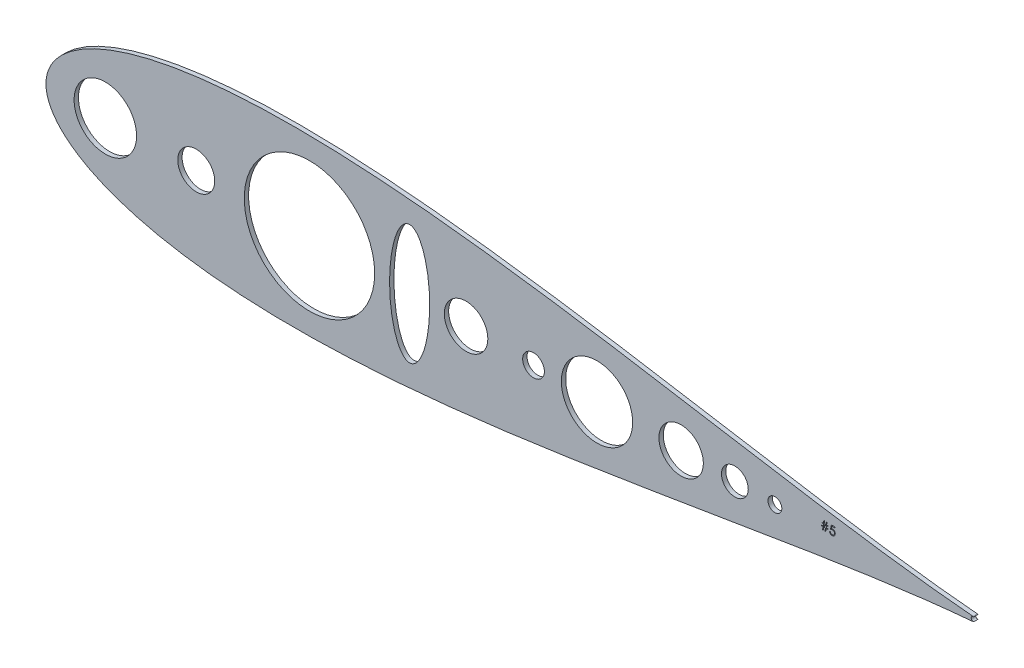
SolidWorks part; units mm, degrees
material "Balsa"
ref_plane "Front Plane" through (0, 0, 0) normal (0, 0, 1) x (1, 0, 0)
ref_plane "Top Plane" through (0, 0, 0) normal (0, 1, 0) x (1, 0, 0)
ref_plane "Right Plane" through (0, 0, 0) normal (1, 0, 0) x (0, 0, -1)
sketch "Sketch2" plane through (0, 0, 0) normal (0, 0, 1) x (1, 0, 0)
  line L0 (368.5896, 3.2313) -> (368.5896, 2.9057)
  line L1 (368.5896, 2.9057) -> (367.6188, 2.9057)
  line L2 (367.6188, 2.9057) -> (367.3552, 1.1472)
  line L3 (367.3552, 1.1472) -> (366.9614, 1.1472)
  line L4 (366.9614, 1.1472) -> (367.2249, 2.9057)
  line L5 (367.2249, 2.9057) -> (366.1859, 2.9057)
  line L6 (366.1859, 2.9057) -> (365.9224, 1.1472)
  line L7 (365.9224, 1.1472) -> (365.5285, 1.1472)
  line L8 (365.5285, 1.1472) -> (365.7921, 2.9057)
  line L9 (365.7921, 2.9057) -> (364.9424, 2.9057)
  line L10 (364.9424, 2.9057) -> (364.9424, 3.2313)
  line L11 (364.9424, 3.2313) -> (365.841, 3.2313)
  line L12 (365.841, 3.2313) -> (366.017, 4.4036)
  line L13 (366.017, 4.4036) -> (365.0727, 4.4036)
  line L14 (365.0727, 4.4036) -> (365.0727, 4.7293)
  line L15 (365.0727, 4.7293) -> (366.0659, 4.7293)
  line L16 (366.0659, 4.7293) -> (366.3101, 6.3575)
  line L17 (366.3101, 6.3575) -> (366.7029, 6.3575)
  line L18 (366.7029, 6.3575) -> (366.4587, 4.7293)
  line L19 (366.4587, 4.7293) -> (367.4987, 4.7293)
  line L20 (367.4987, 4.7293) -> (367.7429, 6.3575)
  line L21 (367.7429, 6.3575) -> (368.1357, 6.3575)
  line L22 (368.1357, 6.3575) -> (367.8915, 4.7293)
  line L23 (367.8915, 4.7293) -> (368.7198, 4.7293)
  line L24 (368.7198, 4.7293) -> (368.7198, 4.4036)
  line L25 (368.7198, 4.4036) -> (367.8426, 4.4036)
  line L26 (367.8426, 4.4036) -> (367.6676, 3.2313)
  line L27 (367.6676, 3.2313) -> (368.5896, 3.2313)
  line L28 (367.4498, 4.4036) -> (366.4098, 4.4036)
  line L29 (366.4098, 4.4036) -> (366.2348, 3.2313)
  line L30 (366.2348, 3.2313) -> (367.2738, 3.2313)
  line L31 (367.2738, 3.2313) -> (367.4498, 4.4036)
  line L32 (372.7578, 6.2272) -> (372.7578, 5.7062)
  line L33 (372.7578, 5.7062) -> (371.0298, 5.7062)
  line L34 (371.0298, 5.7062) -> (370.7561, 4.37)
  line L35 (370.7561, 4.37) -> (370.9179, 4.4128)
  line L36 (370.9179, 4.4128) -> (371.0716, 4.4443)
  line L37 (371.0716, 4.4443) -> (371.2171, 4.4627)
  line L38 (371.2171, 4.4627) -> (371.3545, 4.4688)
  line L39 (371.3545, 4.4688) -> (371.5244, 4.4616)
  line L40 (371.5244, 4.4616) -> (371.6872, 4.4392)
  line L41 (371.6872, 4.4392) -> (371.8419, 4.4026)
  line L42 (371.8419, 4.4026) -> (371.9895, 4.3517)
  line L43 (371.9895, 4.3517) -> (372.1289, 4.2866)
  line L44 (372.1289, 4.2866) -> (372.2602, 4.2062)
  line L45 (372.2602, 4.2062) -> (372.3843, 4.1116)
  line L46 (372.3843, 4.1116) -> (372.5013, 4.0017)
  line L47 (372.5013, 4.0017) -> (372.6072, 3.8806)
  line L48 (372.6072, 3.8806) -> (372.6988, 3.7523)
  line L49 (372.6988, 3.7523) -> (372.7771, 3.615)
  line L50 (372.7771, 3.615) -> (372.8402, 3.4705)
  line L51 (372.8402, 3.4705) -> (372.8901, 3.3168)
  line L52 (372.8901, 3.3168) -> (372.9247, 3.155)
  line L53 (372.9247, 3.155) -> (372.946, 2.9851)
  line L54 (372.946, 2.9851) -> (372.9532, 2.807)
  line L55 (372.9532, 2.807) -> (372.9491, 2.6828)
  line L56 (372.9491, 2.6828) -> (372.9389, 2.5607)
  line L57 (372.9389, 2.5607) -> (372.9206, 2.4416)
  line L58 (372.9206, 2.4416) -> (372.8952, 2.3246)
  line L59 (372.8952, 2.3246) -> (372.8626, 2.2106)
  line L60 (372.8626, 2.2106) -> (372.8229, 2.0997)
  line L61 (372.8229, 2.0997) -> (372.7751, 1.9908)
  line L62 (372.7751, 1.9908) -> (372.7211, 1.884)
  line L63 (372.7211, 1.884) -> (372.6611, 1.7822)
  line L64 (372.6611, 1.7822) -> (372.595, 1.6866)
  line L65 (372.595, 1.6866) -> (372.5247, 1.597)
  line L66 (372.5247, 1.597) -> (372.4494, 1.5136)
  line L67 (372.4494, 1.5136) -> (372.368, 1.4362)
  line L68 (372.368, 1.4362) -> (372.2815, 1.365)
  line L69 (372.2815, 1.365) -> (372.191, 1.2999)
  line L70 (372.191, 1.2999) -> (372.0943, 1.2408)
  line L71 (372.0943, 1.2408) -> (371.9935, 1.1879)
  line L72 (371.9935, 1.1879) -> (371.8887, 1.1432)
  line L73 (371.8887, 1.1432) -> (371.7809, 1.1045)
  line L74 (371.7809, 1.1045) -> (371.6689, 1.0729)
  line L75 (371.6689, 1.0729) -> (371.5529, 1.0485)
  line L76 (371.5529, 1.0485) -> (371.4328, 1.0312)
  line L77 (371.4328, 1.0312) -> (371.3087, 1.02)
  line L78 (371.3087, 1.02) -> (371.1815, 1.017)
  line L79 (371.1815, 1.017) -> (371.0298, 1.0231)
  line L80 (371.0298, 1.0231) -> (370.8843, 1.0424)
  line L81 (370.8843, 1.0424) -> (370.7449, 1.0729)
  line L82 (370.7449, 1.0729) -> (370.6116, 1.1167)
  line L83 (370.6116, 1.1167) -> (370.4844, 1.1727)
  line L84 (370.4844, 1.1727) -> (370.3633, 1.2419)
  line L85 (370.3633, 1.2419) -> (370.2473, 1.3223)
  line L86 (370.2473, 1.3223) -> (370.1384, 1.4159)
  line L87 (370.1384, 1.4159) -> (370.0377, 1.5197)
  line L88 (370.0377, 1.5197) -> (369.9481, 1.6306)
  line L89 (369.9481, 1.6306) -> (369.8687, 1.7486)
  line L90 (369.8687, 1.7486) -> (369.7995, 1.8748)
  line L91 (369.7995, 1.8748) -> (369.7415, 2.0071)
  line L92 (369.7415, 2.0071) -> (369.6947, 2.1475)
  line L93 (369.6947, 2.1475) -> (369.6581, 2.2951)
  line L94 (369.6581, 2.2951) -> (369.6316, 2.4498)
  line L95 (369.6316, 2.4498) -> (370.0875, 2.4498)
  line L96 (370.0875, 2.4498) -> (370.1242, 2.3053)
  line L97 (370.1242, 2.3053) -> (370.171, 2.176)
  line L98 (370.171, 2.176) -> (370.229, 2.06)
  line L99 (370.229, 2.06) -> (370.2972, 1.9583)
  line L100 (370.2972, 1.9583) -> (370.3775, 1.8687)
  line L101 (370.3775, 1.8687) -> (370.4702, 1.7883)
  line L102 (370.4702, 1.7883) -> (370.575, 1.7161)
  line L103 (370.575, 1.7161) -> (370.692, 1.654)
  line L104 (370.692, 1.654) -> (370.8161, 1.6031)
  line L105 (370.8161, 1.6031) -> (370.9444, 1.5675)
  line L106 (370.9444, 1.5675) -> (371.0746, 1.5451)
  line L107 (371.0746, 1.5451) -> (371.2079, 1.538)
  line L108 (371.2079, 1.538) -> (371.3382, 1.5441)
  line L109 (371.3382, 1.5441) -> (371.4634, 1.5614)
  line L110 (371.4634, 1.5614) -> (371.5845, 1.5899)
  line L111 (371.5845, 1.5899) -> (371.7005, 1.6306)
  line L112 (371.7005, 1.6306) -> (371.8114, 1.6815)
  line L113 (371.8114, 1.6815) -> (371.9182, 1.7456)
  line L114 (371.9182, 1.7456) -> (372.02, 1.8199)
  line L115 (372.02, 1.8199) -> (372.1177, 1.9064)
  line L116 (372.1177, 1.9064) -> (372.2062, 2.001)
  line L117 (372.2062, 2.001) -> (372.2836, 2.1018)
  line L118 (372.2836, 2.1018) -> (372.3487, 2.2086)
  line L119 (372.3487, 2.2086) -> (372.4026, 2.3205)
  line L120 (372.4026, 2.3205) -> (372.4443, 2.4386)
  line L121 (372.4443, 2.4386) -> (372.4739, 2.5617)
  line L122 (372.4739, 2.5617) -> (372.4912, 2.691)
  line L123 (372.4912, 2.691) -> (372.4973, 2.8263)
  line L124 (372.4973, 2.8263) -> (372.4922, 2.9484)
  line L125 (372.4922, 2.9484) -> (372.4769, 3.0644)
  line L126 (372.4769, 3.0644) -> (372.4505, 3.1743)
  line L127 (372.4505, 3.1743) -> (372.4138, 3.2781)
  line L128 (372.4138, 3.2781) -> (372.367, 3.3769)
  line L129 (372.367, 3.3769) -> (372.31, 3.4695)
  line L130 (372.31, 3.4695) -> (372.2418, 3.556)
  line L131 (372.2418, 3.556) -> (372.1635, 3.6363)
  line L132 (372.1635, 3.6363) -> (372.077, 3.7096)
  line L133 (372.077, 3.7096) -> (371.9823, 3.7727)
  line L134 (371.9823, 3.7727) -> (371.8816, 3.8256)
  line L135 (371.8816, 3.8256) -> (371.7737, 3.8704)
  line L136 (371.7737, 3.8704) -> (371.6587, 3.904)
  line L137 (371.6587, 3.904) -> (371.5366, 3.9284)
  line L138 (371.5366, 3.9284) -> (371.4084, 3.9427)
  line L139 (371.4084, 3.9427) -> (371.272, 3.9477)
  line L140 (371.272, 3.9477) -> (371.154, 3.9437)
  line L141 (371.154, 3.9437) -> (371.0288, 3.9315)
  line L142 (371.0288, 3.9315) -> (370.8986, 3.9111)
  line L143 (370.8986, 3.9111) -> (370.7612, 3.8826)
  line L144 (370.7612, 3.8826) -> (370.6187, 3.846)
  line L145 (370.6187, 3.846) -> (370.4691, 3.8012)
  line L146 (370.4691, 3.8012) -> (370.3145, 3.7483)
  line L147 (370.3145, 3.7483) -> (370.1526, 3.6872)
  line L148 (370.1526, 3.6872) -> (370.6737, 6.2272)
  line L149 (370.6737, 6.2272) -> (372.7578, 6.2272)
  circle A0 centre (-53.0543, 0) radius 18.2309
  circle A1 centre (337.7159, 0) radius 4.0377
  circle A2 centre (314.3539, 0) radius 7.8218
  circle A3 centre (282.9982, 0) radius 12.9578
  circle A4 centre (233.8937, 0) radius 20.8135
  circle A5 centre (196.85, 0) radius 6.35
  circle A6 centre (157.48, 0) radius 12.7
  circle A7 centre (66.0899, 0) radius 38.053
  circle A8 centre (0, 0) radius 10.795
  arc A9 (453.7173, 1.2315) -> (453.7153, -1.2323) centre (453.5388, -0.0003) ccw
  arc A10 (453.7173, 1.2315) -> (453.3083, 1.3321) centre (453.1975, 0) ccw
  arc A11 (453.3083, -1.3321) -> (453.7153, -1.2323) centre (453.1975, 0) ccw
  ellipse E0 centre (124.5387, 0) end of major axis (124.5387, -34.948) minor radius 11.7082
  spline S0 degree 3 poles (453.3083, 1.3321) (452.8726, 1.3683) (449.589, 1.6449) (443.1226, 2.2426) (433.524, 3.2411) (422.8819, 4.4663) (411.2361, 5.9257) (398.6411, 7.6206) (385.1512, 9.5474) (370.825, 11.6959) (355.7232, 14.0511) (339.9092, 16.5917) (323.4482, 19.2916) (306.4075, 22.1197) (288.856, 25.0402) (270.8643, 28.0136) (252.5043, 30.9967) (233.8492, 33.9438) (214.9738, 36.8068) (195.9541, 39.5365) (176.8673, 42.083) (157.7923, 44.3967) (138.809, 46.4289) (119.9989, 48.1326) (101.4449, 49.4634) (83.231, 50.3803) (65.4429, 50.8463) (48.1673, 50.829) (31.4925, 50.301) (15.508, 49.2416) (0.3051, 47.6356) (-14.0235, 45.4755) (-27.3821, 42.7608) (-39.6719, 39.5004) (-50.7891, 35.7134) (-60.6226, 31.4337) (-69.0532, 26.7179) (-75.9548, 21.6616) (-81.2112, 16.4301) (-84.7699, 11.2999) (-86.7543, 6.6715) (-87.5557, 2.9586) (-87.7382, 0) (-87.5557, -2.9586) (-86.7543, -6.6715) (-84.7699, -11.2999) (-81.2112, -16.4301) (-75.9548, -21.6616) (-69.0532, -26.7179) (-60.6226, -31.4337) (-50.7891, -35.7134) (-39.6719, -39.5004) (-27.3821, -42.7608) (-14.0235, -45.4755) (0.3051, -47.6356) (15.508, -49.2416) (31.4925, -50.301) (48.1673, -50.829) (65.4429, -50.8463) (83.231, -50.3803) (101.4449, -49.4634) (119.9989, -48.1326) (138.809, -46.4289) (157.7923, -44.3967) (176.8673, -42.083) (195.9541, -39.5365) (214.9738, -36.8068) (233.8492, -33.9438) (252.5043, -30.9967) (270.8643, -28.0136) (288.856, -25.0402) (306.4075, -22.1197) (323.4482, -19.2916) (339.9092, -16.5917) (355.7232, -14.0511) (370.825, -11.6959) (385.1512, -9.5474) (398.6411, -7.6206) (411.2361, -5.9257) (422.8819, -4.4663) (433.524, -3.2411) (443.1226, -2.2426) (449.589, -1.6449) (452.8726, -1.3683) (453.3083, -1.3321) knots 0.020157 0.020157 0.020157 0.020157 0.021271 0.028553 0.036781 0.04592 0.055932 0.066773 0.078397 0.090755 0.103793 0.117456 0.131686 0.146422 0.1616 0.177156 0.193024 0.209135 0.225421 0.241812 0.258238 0.274629 0.290914 0.307025 0.322893 0.338448 0.353626 0.368361 0.38259 0.396253 0.40929 0.421647 0.43327 0.444109 0.454119 0.463255 0.471479 0.478755 0.485052 0.490344 0.49461 0.497833 0.5 0.502167 0.50539 0.509656 0.514948 0.521245 0.528521 0.536745 0.545881 0.555891 0.56673 0.578353 0.59071 0.603747 0.61741 0.631639 0.646374 0.661552 0.677107 0.692975 0.709086 0.725371 0.741762 0.758188 0.774579 0.790865 0.806976 0.822844 0.8384 0.853578 0.868314 0.882544 0.896207 0.909245 0.921603 0.933227 0.944068 0.95408 0.963219 0.971447 0.978729 0.979843 0.979843 0.979843 0.979843
  dimension "D1" = 21.59
  dimension "D2" = 76.1061
  dimension "D3" = 25.4
  dimension "D4" = 41.627
  dimension "D5" = 12.7
  dimension "D6" = 25.9156
  dimension "D7" = 15.6437
  dimension "D8" = 8.0754
  dimension "D11" = 36.4618
  dimension "D9" = 11.7082
  dimension "D10" = 34.948
extrude "Boss-Extrude1" add sketch "Sketch2" along normal blind 2.54 contours A10 S0 A11 A9 L148 L149 L32 L33 L34 L35 L36 L37 L38 L39 L40 L41 L42 L43 L44 L45 L46 L47 L48 L49 L50 L51 L52 L53 L54 L55 L56 L57 L58 L59 L60 L61 L62 L63 L64 L65 L66 L67 L68 L69 L70 L71 L72 L73 L74 L75
equation "\"ROD DIAM\"= .85"
